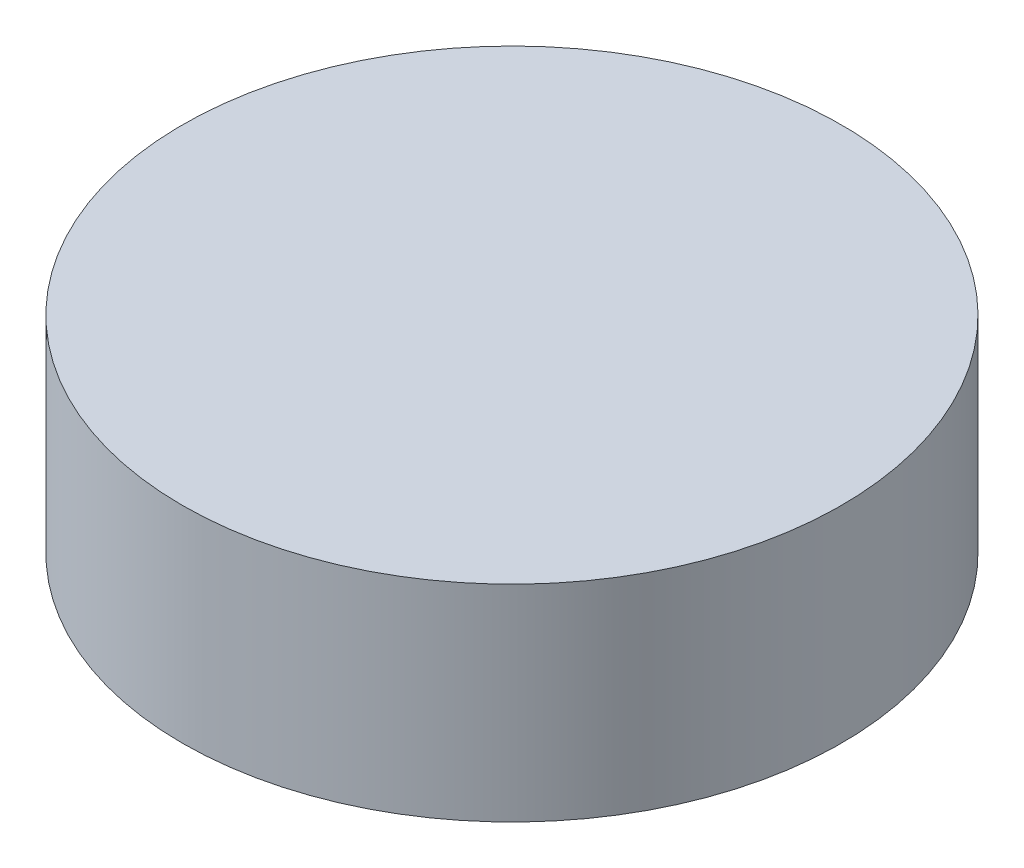
SolidWorks part; units mm, degrees
ref_plane "Front Plane" through (0, 0, 0) normal (0, 0, 1) x (1, 0, 0)
ref_plane "Top Plane" through (0, 0, 0) normal (0, 1, 0) x (1, 0, 0)
ref_plane "Right Plane" through (0, 0, 0) normal (1, 0, 0) x (0, 0, -1)
sketch "Sketch1" plane through (0, 0, 0) normal (0, 1, 0) x (1, 0, 0)
  circle A0 centre (0, 0) radius 0.4
extrude "Boss-Extrude1" add sketch "Sketch1" along normal blind 0.25
